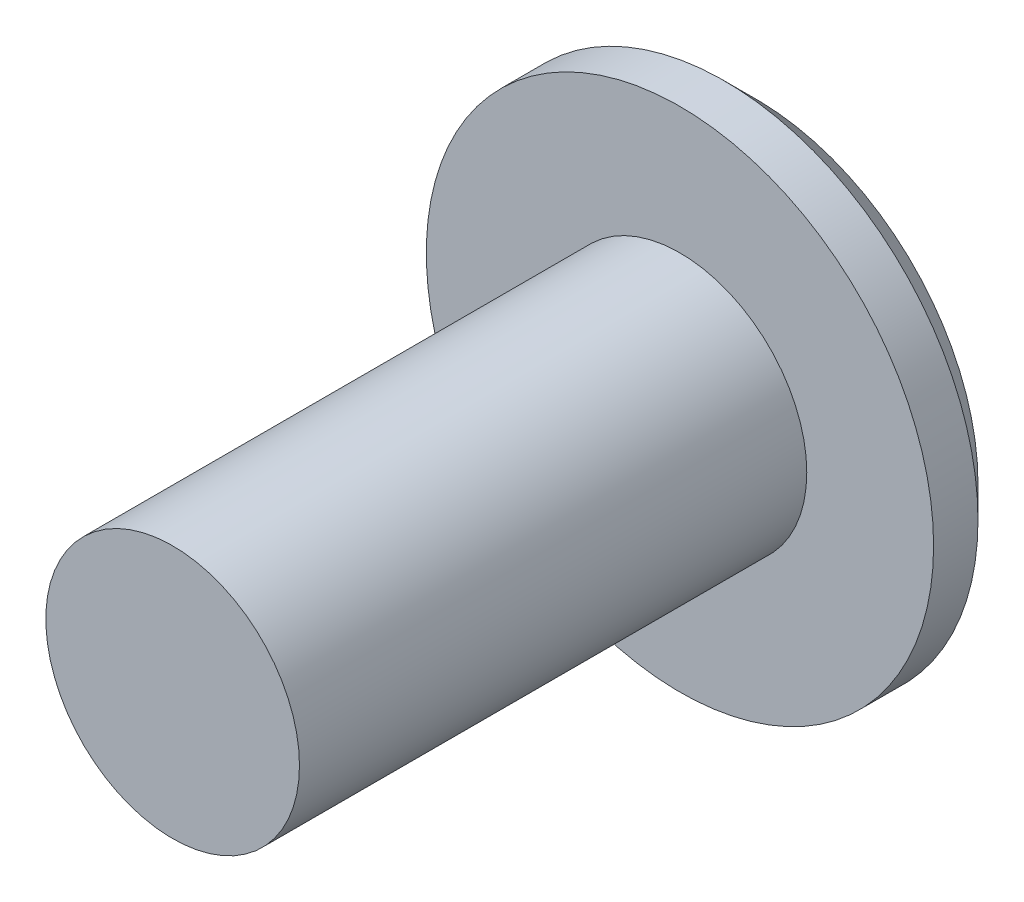
SolidWorks part; units mm, degrees
ref_plane "前视基准面" through (0, 0, 0) normal (0, 0, 1) x (1, 0, 0)
ref_plane "上视基准面" through (0, 0, 0) normal (0, 1, 0) x (1, 0, 0)
ref_plane "右视基准面" through (0, 0, 0) normal (1, 0, 0) x (0, 0, -1)
sketch "草图1" plane through (0, 0, 0) normal (0, 0, 1) x (1, 0, 0)
  circle A0 centre (0, 0) radius 4
  dimension "D1" = 8
extrude "凸台-拉伸1" add sketch "草图1" along normal blind 1.2
chamfer "倒角1" distance 0.5 angle 45 1 edges at (4, 0, 0)
sketch "草图3" plane through (0, 0, 1.2) normal (0, 0, 1) x (1, 0, 0)
  circle A0 centre (0, 0) radius 2
  dimension "D1" = 4
extrude "凸台-拉伸2" add sketch "草图3" along normal blind 8
sketch "草图4" plane through (0, 0, 0) normal (0, 0, -1) x (-1, 0, 0)
  line L1 (0, 1.4434) -> (-1.25, 0.7217)
  line L2 (-1.25, 0.7217) -> (-1.25, -0.7217)
  line L3 (-1.25, -0.7217) -> (0, -1.4434)
  line L4 (0, -1.4434) -> (1.25, -0.7217)
  line L5 (1.25, -0.7217) -> (1.25, 0.7217)
  line L6 (1.25, 0.7217) -> (0, 1.4434)
  circle A0 centre (0, 0) radius 1.25 construction
  dimension "D1" = 2.5
extrude "切除-拉伸1" cut sketch "草图4" against normal blind 2.2
